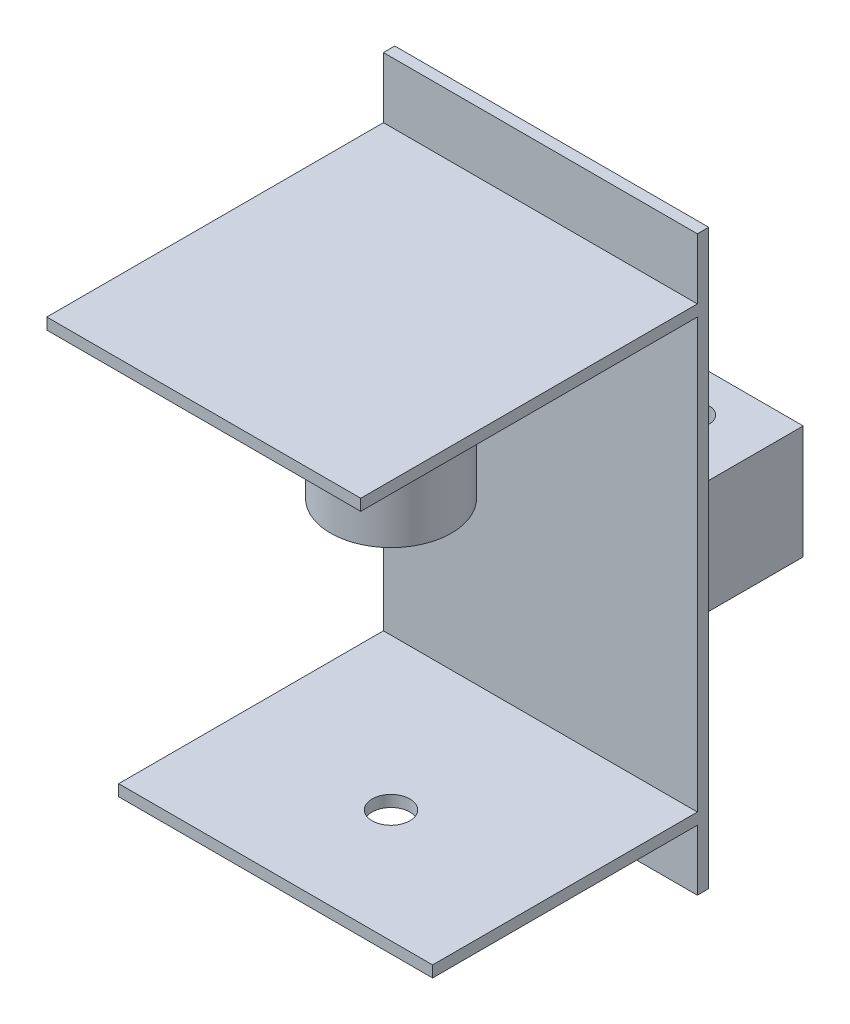
SolidWorks part; units mm, degrees
ref_plane "Front Plane" through (0, 0, 0) normal (0, 0, 1) x (1, 0, 0)
ref_plane "Top Plane" through (0, 0, 0) normal (0, 1, 0) x (1, 0, 0)
ref_plane "Right Plane" through (0, 0, 0) normal (1, 0, 0) x (0, 0, -1)
sketch "Sketch1" plane through (0, 0, 0) normal (0, 0, 1) x (1, 0, 0)
  line L1 (0, 0) -> (83, 0)
  line L2 (0, 0) -> (0, 151.45)
  line L3 (0, 151.45) -> (83, 151.45)
  line L4 (83, 0) -> (83, 151.45)
  dimension "D1" = 151.45
  dimension "D2" = 83
extrude "Boss-Extrude1" add sketch "Sketch1" along normal blind 3
ref_plane "Plane1" through (0, 16.05, 0) normal (0, -1, 0) x (-1, 0, 0)
sketch "Sketch2" plane through (0, 16.05, 0) normal (0, -1, 0) x (-1, 0, 0)
  line L1 (0, -3) -> (-83, -3)
  line L2 (0, -3) -> (0, -73)
  line L3 (0, -73) -> (-83, -73)
  line L4 (-83, -3) -> (-83, -73)
  dimension "D2" = 70
extrude "Boss-Extrude2" add sketch "Sketch2" against normal blind 3
ref_plane "Plane2" through (0, 75.725, 0) normal (0, 1, 0) x (1, 0, 0)
mirror "Mirror1" about plane through (0, 75.725, 0) normal (0, 1, 0) of "Boss-Extrude2"
sketch "Sketch3" plane through (0, 135.4, 0) normal (0, 1, 0) x (1, 0, 0)
  line L0 (83, -3) -> (83, -73) construction
  line L3 (0, -3) -> (83, -3)
  line L4 (0, -3) -> (0, -92)
  line L5 (0, -92) -> (83, -92)
  line L6 (83, -3) -> (83, -92)
  circle A0 centre (42, -43) radius 2.5
  dimension "D1" = 5
  dimension "D2" = 41
  dimension "D3" = 89
  dimension "D4" = 49
extrude "Boss-Extrude3" add sketch "Sketch3" against normal blind 3 contours L4 L3 L6 L5
ref_plane "Plane3" through (0, 88.45, 0) normal (0, 1, 0) x (1, 0, 0)
sketch "Sketch6" plane through (0, 88.45, 0) normal (0, 1, 0) x (1, 0, 0)
  line L0 (83, 0) -> (0, 0) construction
  line L1 (83, -3) -> (83, 0) construction
  line L2 (0, -3) -> (0, 0) construction
  line L3 (21.979, 28.4079) -> (21.979, 10.3201) construction
  line L4 (4.979, 28) -> (38.979, 28)
  line L5 (4.979, 28) -> (4.979, 0)
  line L6 (4.979, 0) -> (38.979, 0)
  line L7 (38.979, 28) -> (38.979, 0)
  line L8 (43.98, 30) -> (77.98, 30)
  line L9 (43.98, 30) -> (43.98, 0)
  line L10 (43.98, 0) -> (77.98, 0)
  line L11 (77.98, 30) -> (77.98, 0)
  line L12 (60.98, 26.9273) -> (60.98, 9.1275) construction
  circle A0 centre (21.979, 18) radius 4.15
  circle A1 centre (60.98, 18) radius 4.15
  dimension "D1" = 8.3
  dimension "D2" = 8.3
  dimension "D3" = 18
  dimension "D4" = 22.02
  dimension "D5" = 18
  dimension "D6" = 21.979
  dimension "D7" = 17
  dimension "D8" = 34
  dimension "D9" = 0
  dimension "D10" = 34
  dimension "D11" = 17
  dimension "D12" = 30
extrude "Boss-Extrude6" add sketch "Sketch6" against normal blind 30
sketch "Sketch7" plane through (0, 132.4, 0) normal (0, -1, 0) x (1, 0, 0)
  line L4 (0, 92) -> (0, 3)
  line L5 (0, 3) -> (83, 3)
  line L6 (83, 3) -> (83, 92)
  line L7 (83, 92) -> (0, 92)
  line L8 (0, 92) -> (0, 3)
  line L9 (0, 3) -> (83, 3)
  line L10 (83, 3) -> (83, 92)
  line L11 (83, 92) -> (0, 92)
  circle A0 centre (42, 43) radius 16
  circle A1 centre (42, 43) radius 7
  circle A3 centre (42, 43) radius 2.5
  circle A4 centre (42, 43) radius 15
  dimension "D3" = 32
  dimension "D1" = 0
extrude "Boss-Extrude7" add sketch "Sketch7" along normal blind 42 contours A4 | A0
sketch "Sketch8" plane through (0, 19.05, 0) normal (0, 1, 0) x (1, 0, 0)
  line L4 (0, -3) -> (0, -73)
  line L5 (0, -73) -> (83, -73)
  line L6 (83, -73) -> (83, -3)
  line L7 (83, -3) -> (0, -3)
  line L8 (0, -3) -> (0, -73)
  line L9 (0, -73) -> (83, -73)
  line L10 (83, -73) -> (83, -3)
  line L11 (83, -3) -> (0, -3)
  circle A0 centre (42, -43) radius 15 construction
  circle A1 centre (42, -43) radius 15
  circle A2 centre (42, -43) radius 5
  dimension "D1" = 0
extrude "Cut-Extrude1" cut sketch "Sketch8" against normal through all contours A2
